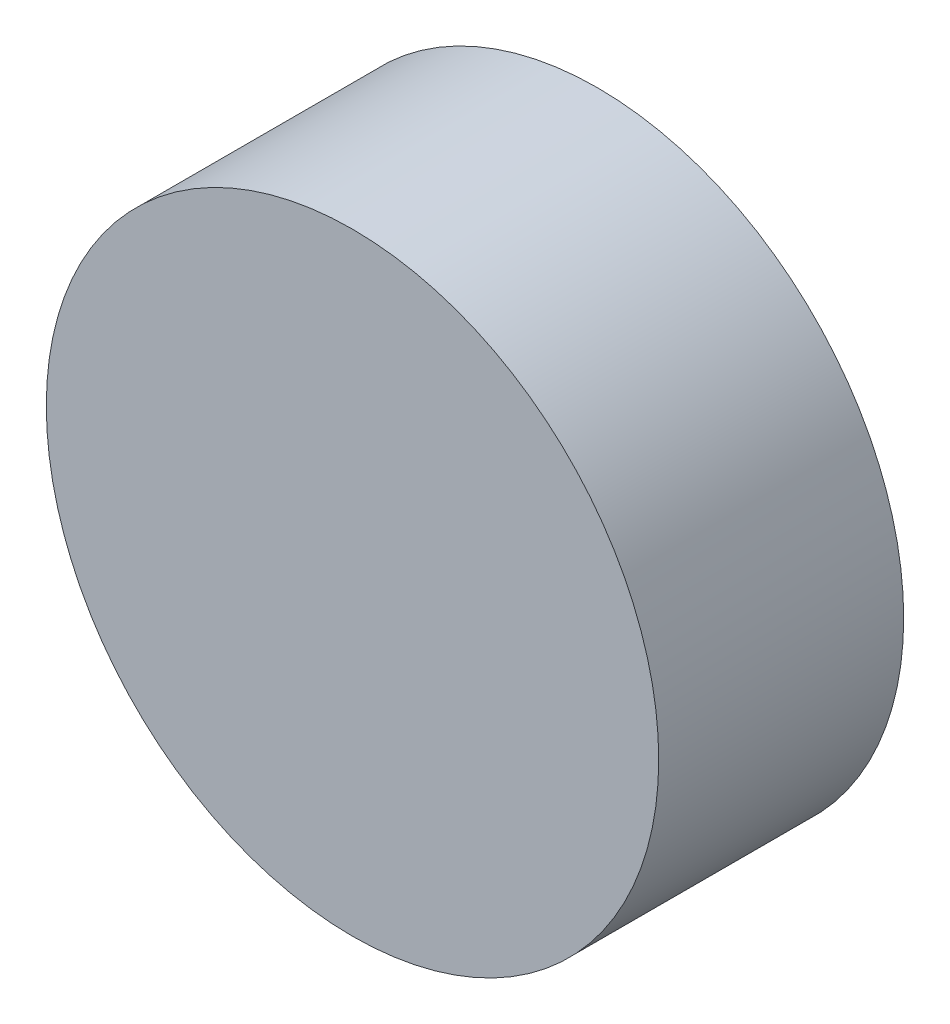
SolidWorks part; units mm, degrees
ref_plane "Front Plane" through (0, 0, 0) normal (0, 0, 1) x (1, 0, 0)
ref_plane "Top Plane" through (0, 0, 0) normal (0, 1, 0) x (1, 0, 0)
ref_plane "Right Plane" through (0, 0, 0) normal (1, 0, 0) x (0, 0, -1)
sketch "Sketch1" plane through (0, 0, 0) normal (0, 0, 1) x (1, 0, 0)
  circle A0 centre (0, 0) radius 2.5
  dimension "D1" = 5
extrude "Boss-Extrude1" add sketch "Sketch1" along normal blind 2
